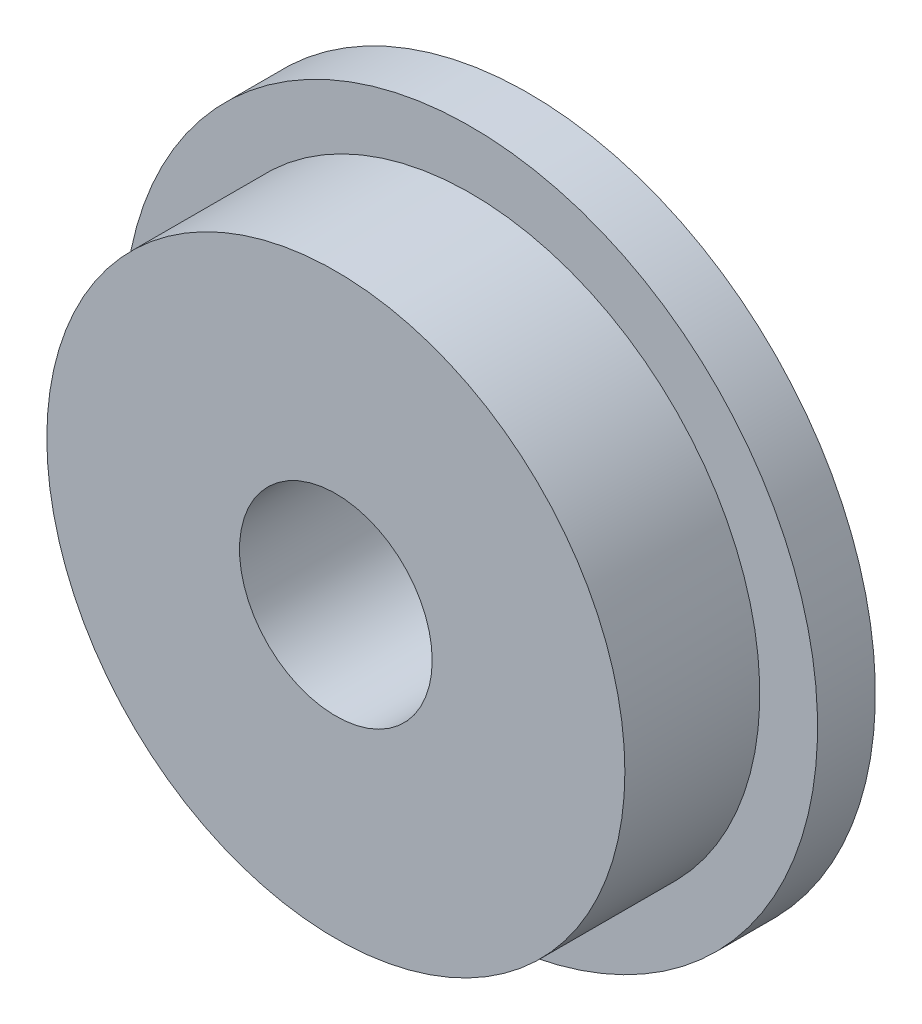
SolidWorks part; units mm, degrees
material "Сталь ШХ15 ГОСТ 801-78"
ref_plane "Plane1" through (0, 0, 0) normal (0, 0, 1) x (1, 0, 0)
ref_plane "Plane2" through (0, 0, 0) normal (0, 1, 0) x (1, 0, 0)
ref_plane "Plane3" through (0, 0, 0) normal (1, 0, 0) x (0, 0, -1)
sketch "Эскиз1" plane through (0, 0, 0) normal (0, 0, 1) x (1, 0, 0)
  circle A0 centre (0, 0) radius 3
  dimension "D1" = 6
extrude "Бобышка-Вытянуть1" add sketch "Эскиз1" along normal blind 2 contours A0
sketch "Эскиз3" plane through (0, 0, 0) normal (0, 0, -1) x (-1, 0, 0)
  circle A0 centre (0, 0) radius 3.6
  dimension "D1" = 7.2
extrude "Бобышка-Вытянуть2" add sketch "Эскиз3" against normal blind 0.6
sketch "Эскиз4" plane through (0, 0, 2) normal (0, 0, 1) x (1, 0, 0)
  circle A0 centre (0, 0) radius 1
  dimension "D1" = 2
extrude "Вырез-Вытянуть1" cut sketch "Эскиз4" against normal through all both and the other way through all
